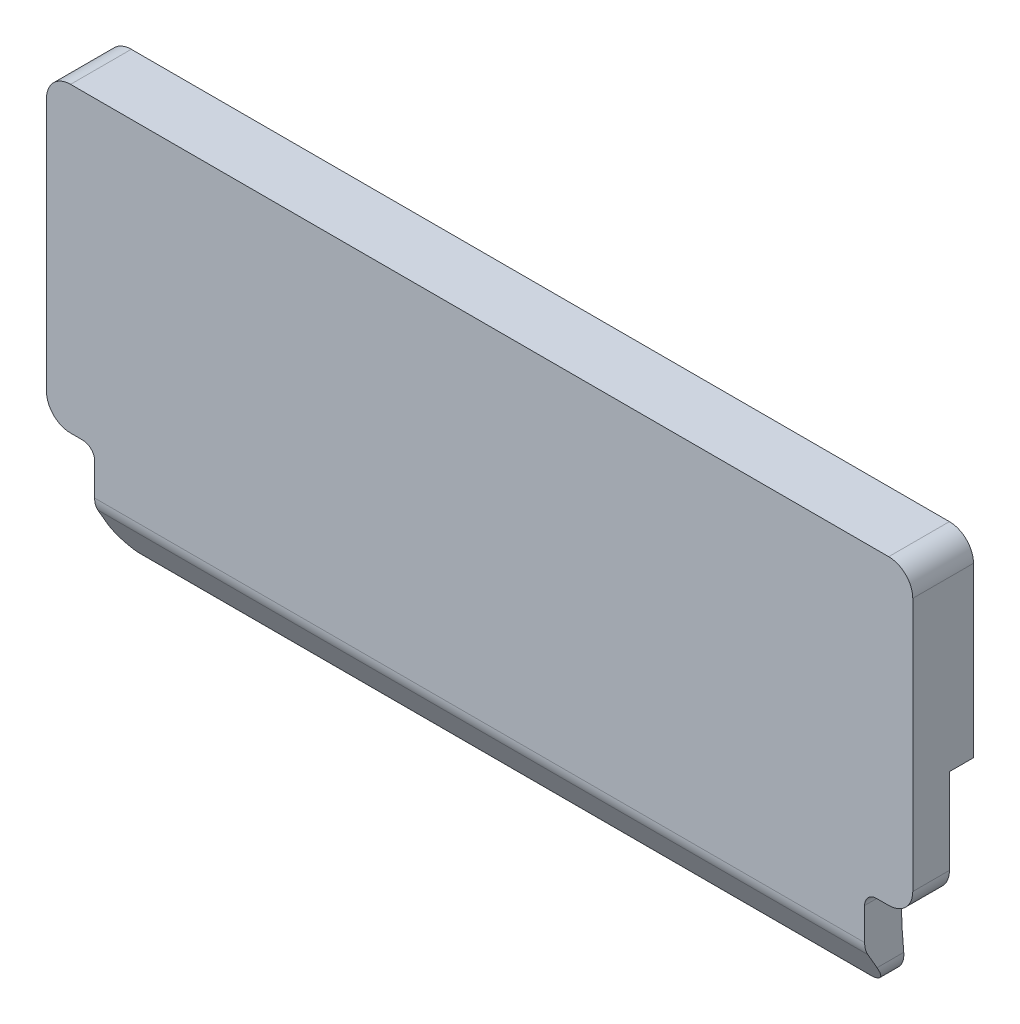
SolidWorks part; units mm, degrees
ref_plane "Front Plane" through (0, 0, 0) normal (0, 0, 1) x (1, 0, 0)
ref_plane "Top Plane" through (0, 0, 0) normal (0, 1, 0) x (1, 0, 0)
ref_plane "Right Plane" through (0, 0, 0) normal (1, 0, 0) x (0, 0, -1)
sketch "Sketch1" plane through (0, 0, 0) normal (0, 0, 1) x (1, 0, 0)
  line L1 (-18, 9.3045) -> (-18, 10.3045)
  line L2 (18, 9.3035) -> (18, 17.3035)
  line L3 (18, 9.3035) -> (18, 6.7512)
  line L4 (-18, 10.3045) -> (-18, 17.3035)
  line L5 (17, 5.7512) -> (16.5, 5.7512)
  line L6 (16, 5.2512) -> (16, 2.7512)
  line L7 (15, 1.7512) -> (-15, 1.7512)
  line L9 (17, 18.3035) -> (-17, 18.3035)
  line L10 (-16, 5.2512) -> (-16, 2.7512)
  line L11 (-17, 5.7512) -> (-16.5, 5.7512)
  line L12 (-18, 9.3045) -> (-18, 6.7512)
  arc A0 (18, 6.7512) -> (17, 5.7512) centre (17, 6.7512) cw
  arc A2 (16, 2.7512) -> (15, 1.7512) centre (15, 2.7512) cw
  arc A3 (16, 5.2512) -> (16.5, 5.7512) centre (16.5, 5.2512) cw
  arc A4 (-16, 5.2512) -> (-16.5, 5.7512) centre (-16.5, 5.2512) ccw
  arc A5 (-16, 2.7512) -> (-15, 1.7512) centre (-15, 2.7512) ccw
  arc A7 (-18, 6.7512) -> (-17, 5.7512) centre (-17, 6.7512) ccw
  arc A8 (18, 17.3035) -> (17, 18.3035) centre (17, 17.3035) ccw
  arc A9 (-18, 17.3035) -> (-17, 18.3035) centre (-17, 17.3035) cw
  point P37 (-16, 5.7512)
  point P38 (-18, 10.3045)
  point P39 (-18, 5.7512)
  dimension "D1" = 1
extrude "Boss-Extrude1" add sketch "Sketch1" along normal blind 1.5 and the other way blind 1.2
sketch "Sketch3" plane through (18, 0, 0) normal (1, 0, 0) x (0, 0, -1)
  line L1 (0.0238, 5.7545) -> (0.0238, 10.3045)
  line L4 (0.0238, 10.3045) -> (1.0238, 10.3045)
  line L7 (-1.5, 3.6459) -> (-1.5, 1.7512)
  line L8 (-1.5, 3.6459) -> (-1.5, 1.7512)
  line L9 (0.2373, 1.7512) -> (1.2709, 1.7512)
  line L10 (1.2, 1.7512) -> (-1.5, 1.7512) construction
  line L12 (1.2709, 1.7512) -> (1.2709, 10.3045)
  line L16 (-0.435, 1.8012) -> (-1.5, 3.6459)
  line L17 (-1.5, 1.7512) -> (-0.3061, 1.7512)
  line L18 (0.0238, 10.3051) -> (0.0238, 10.3045)
  line L19 (1, 10.3051) -> (-1.5, 10.3051) construction
  line L20 (1.0238, 10.3045) -> (1.0238, 22.6808)
  line L21 (1.2709, 10.3045) -> (1.2709, 10.3051)
  line L22 (-1.5, 1.7512) -> (-0.4061, 1.7512)
  line L23 (-1.5, 3.6459) -> (-1.5, 1.7512)
  line L24 (0.0238, 10.3045) -> (1.0238, 10.3045)
  line L25 (-0.3484, 1.7512) -> (-0.3061, 1.7512)
  arc A0 (0.0238, 5.7545) -> (0.2373, 1.7512) centre (25.9469, 5.1296) ccw
  arc A4 (1.0238, 22.6808) -> (1.2709, 10.3051) centre (1.0238, 16.4905) cw
  arc A5 (-0.435, 1.8012) -> (-0.3484, 1.7512) centre (-0.3484, 1.8512) ccw
  point P28 (-1.5, 6.7512)
  point P31 (-0.2647, 1.7512)
  dimension "D1" = 4.55
  dimension "D2" = 0.1
extrude "Cut-Extrude1" cut sketch "Sketch3" against normal blind 40 contours L7 L17 L16 | A4 L20 L1 A0 L9 L12 L21 M27 M13 M12 | L20 L4 L1 M12 M13 M27
sketch "Sketch6" plane through (-18, 0, 0) normal (-1, 0, 0) x (0, 0, 1)
  line L0 (-1.0238, 10.3045) -> (-1.0238, 12.6345)
  line L1 (-1.0238, 17.3035) -> (-1.0238, 10.3045) construction
fillet "Fillet1" radius 1 1 edges at (0, 3.6459, 1.5)
sketch "Sketch7" plane through (-18, 0, 0) normal (-1, 0, 0) x (0, 0, 1)
  line L0 (-1.0238, 10.3045) -> (1.3872, 3.6805)
  line L1 (-1.0238, 10.3045) -> (-1.0238, 12.6345)
  line L2 (-1.0238, 17.3035) -> (-1.0238, 10.3045) construction
sketch "Sketch8" plane through (0, 0, -1.0238) normal (0, 0, -1) x (-1, 0, 0)
  line L1 (0, 10.3045) -> (0, 12.6345)
  line L2 (18, 10.3045) -> (-18, 10.3045) construction
  line L3 (0, 12.6345) -> (0, 13.8645)
  circle A0 centre (0, 13.8645) radius 1.23
sketch "Sketch10" plane through (18, 0, 0) normal (1, 0, 0) x (0, 0, -1)
  line L1 (1.0238, 10.3045) -> (1.0238, 17.3035) construction
  line L2 (1.0238, 13.804) -> (12.7887, 9.5219) construction
sketch "Sketch11" plane through (0, 0, -1.0238) normal (0, 0, -1) x (-1, 0, 0)
  line L0 (0, 10.3045) -> (0, 15.2945)
  line L2 (18, 10.3045) -> (-18, 10.3045) construction
  line L3 (-11, 15.2945) -> (11, 15.2945)
  circle A0 centre (11, 15.2945) radius 1
  circle A1 centre (-11, 15.2945) radius 1
  circle A2 centre (0, 15.2945) radius 2.5
  dimension "D1" = 2
  dimension "D4" = 5
  dimension "D2" = 11
  dimension "D3" = 4.99
sketch "Sketch12" plane through (18, 0, 0) normal (1, 0, 0) x (0, 0, -1)
  line L0 (1.0238, 10.3045) -> (1.0238, 15.2945)
  line L1 (1.0238, 10.3045) -> (1.0238, 17.3035) construction
  line L2 (1.0238, 15.2945) -> (6.2899, 13.3778)
  dimension "D1" = 4.99
ref_plane "Plane1" through (0, 0.8764, 2.4078) normal (0, -0.342, -0.9397) x (1, 0, 0)
sketch "Sketch15" plane through (0, 0.8764, 2.4078) normal (0, -0.342, -0.9397) x (1, 0, 0)
  line L0 (0, -10.0333) -> (0, -15.0333)
  line L1 (-18, -10.0333) -> (18, -10.0333) construction
  circle A1 centre (0, -15.0333) radius 2.45
  dimension "D2" = 4.9
  dimension "D1" = 5
sketch "Sketch16" plane through (0, 0, 0) normal (1, 0, 0) x (0, 0, -1)
  line L0 (1.0238, 10.3045) -> (1.0238, 15.3085)
  line L1 (1.0238, 10.3045) -> (1.0238, 17.3035) construction
  line L2 (1.0238, 15.3085) -> (6.662, 13.2563)
  line L3 (1.0238, 15.3085) -> (1.0238, 12.8065)
  line L5 (6.662, 10.7613) -> (6.662, 13.2563)
  line L6 (6.662, 10.7613) -> (1.0238, 12.8065)
  dimension "D1" = 2.495
revolve "Revolve1" [suppressed] add sketch "Sketch16" angle 360 about L2
sketch "Sketch17" plane through (0, 0, -1.0238) normal (0, 0, -1) x (-1, 0, 0)
sketch "Sketch18" [suppressed] plane through (0, 0, 0) normal (1, 0, 0) x (0, 0, -1)
  line L0 (1.0238, 15.3085) -> (1.0238, 17.8035)
  line L1 (1.0238, 17.3035) -> (1.0238, 18.3035) construction
  line L2 (1.0238, 17.8035) -> (2.632, 17.2251)
  line L4 (1.0238, 15.3085) -> (7.4638, 12.9645)
  line L5 (6.662, 10.7613) -> (8.2657, 15.1676) construction
  line L6 (2.632, 17.2251) -> (1.8279, 15.0158)
  line L7 (1.0238, 12.8065) -> (2.632, 17.2251) construction
  line L8 (2.632, 17.2251) -> (1.0238, 15.3085)
  dimension "D1" = 2.495
ref_plane "Plane2" through (0, 0, -1.0238) normal (0, 0, -1) x (-1, 0, 0)
extrude "Cut-Extrude2" [suppressed] cut sketch "Sketch11" against normal blind 5
sketch "Sketch19" plane through (-18, 0, 0) normal (-1, 0, 0) x (0, 0, 1)
  line L0 (-1.0238, 10.3045) -> (-1.0238, -0.7255)
  line L1 (-1.0238, -0.7255) -> (3.0273, 6.2913)
  dimension "D1" = 150
